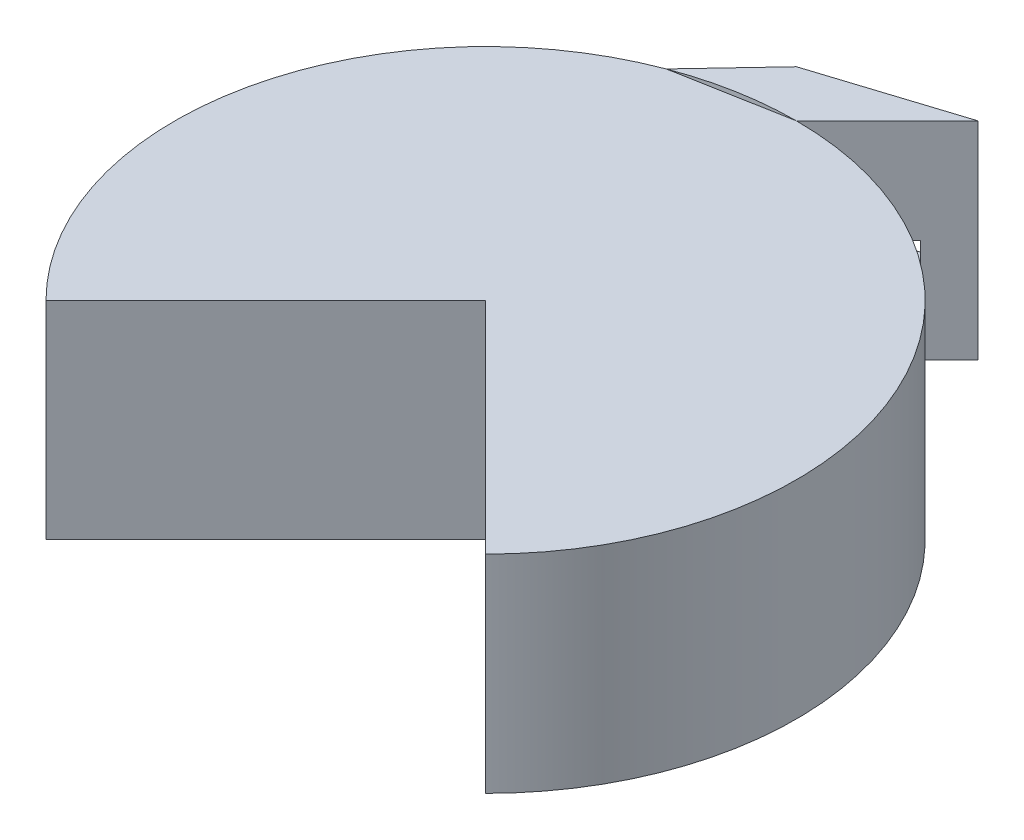
SolidWorks part; units mm, degrees
ref_plane "Front Plane" through (0, 0, 0) normal (0, 0, 1) x (1, 0, 0)
ref_plane "Top Plane" through (0, 0, 0) normal (0, 1, 0) x (1, 0, 0)
ref_plane "Right Plane" through (0, 0, 0) normal (1, 0, 0) x (0, 0, -1)
sketch "Sketch1" plane through (0, 0, 0) normal (0, 1, 0) x (1, 0, 0)
  line L0 (0, 0) -> (-53.033, -53.033)
  line L1 (-53.033, -53.033) -> (0, 0)
  line L2 (53.033, -53.033) -> (0, 0)
  line L3 (0, 0) -> (0, 75)
  line L4 (0, 75) -> (-75, 0)
  line L5 (-75, 0) -> (0, 75)
  line L6 (0, 75) -> (21.9069, 96.9069)
  line L7 (0, 75) -> (-11.3137, 86.3137)
  line L8 (21.9069, 96.9069) -> (-11.3137, 86.3137)
  line L9 (-11.3137, 86.3137) -> (-26.5555, 70.1413)
  line L10 (-26.5555, 70.1413) -> (0, 75)
  circle A0 centre (0, 0) radius 75
  dimension "D1" = 150
  dimension "D2" = 16
  dimension "D3" = 21.9069
extrude "Boss-Extrude2" add sketch "Sketch1" along normal blind 50 contours L2 A0 L3 | L4 A0 L0 L3 | L10 A0 L4 | A0 L7 L9 | L6 L8 L7
sketch "Sketch2" plane through (-26.0271, 0, -81.622) normal (-0.3038, 0, -0.9527) x (-0.9527, 0, 0.3038)
  line L0 (-50.312, 0) -> (-15.4434, 0)
  line L1 (-50.312, 50) -> (-50.312, 25)
  line L2 (-50.312, 50) -> (-50.312, 0) construction
  line L3 (-50.312, 25) -> (-15.4434, 25)
  line L4 (-15.4434, 50) -> (-15.4434, 0) construction
  line L5 (-32.8777, 25) -> (-50.312, 25)
  line L7 (-41.5949, 25) -> (-21.5949, 25)
  line L8 (-41.5949, 25) -> (-41.5949, 19)
  line L9 (-41.5949, 19) -> (-21.5949, 19)
  line L10 (-21.5949, 25) -> (-21.5949, 19)
  dimension "D1" = 6
  dimension "D2" = 20
  dimension "D3" = 8.7172
extrude "Cut-Extrude1" cut sketch "Sketch2" against normal blind 16 contours L10 L3 L5 L8 L9
sketch "Sketch3" plane through (0, 0, 0) normal (0, -1, 0) x (1, 0, 0)
  line L1 (0, 0) -> (-53.033, 53.033) construction
  circle A1 centre (-38.637, 10.3528) radius 18
  arc A2 (-53.033, 53.033) -> (-26.5555, -70.1413) centre (0, 0) ccw construction
  point P3 (-74.7993, 5.4827)
  dimension "D1" = 20
  dimension "D3" = 40
  dimension "D4" = 36
  dimension "D2" = 20
extrude "Cut-Extrude2" cut sketch "Sketch3" against normal blind 30
sketch "Sketch4" plane through (0, 0, 0) normal (0, -1, 0) x (-1, 0, 0)
  line L0 (0, 4.2351) -> (0, 0)
  line L1 (-53.033, -53.033) -> (0, 0) construction
  circle A1 centre (-38.637, -10.3528) radius 18
  dimension "D3" = 36
  dimension "D1" = 40
  dimension "D2" = 20
extrude "Cut-Extrude3" cut sketch "Sketch4" against normal blind 30 contours A1
sketch "Sketch7" plane through (0, 0, 0) normal (0, -1, 0) x (-1, 0, 0)
  circle A1 centre (38.637, 44.282) radius 15
  dimension "D4" = 30
extrude "Cut-Extrude4" cut sketch "Sketch7" against normal blind 30
sketch "Sketch9" plane through (0, 0, 0) normal (0, -1, 0) x (1, 0, 0)
  line L0 (0, -75) -> (-38.637, -44.282)
  line L1 (-38.637, -44.282) -> (-38.637, -64.282)
  line L2 (-38.637, -64.282) -> (-38.637, -44.282)
  arc A0 (-53.033, 53.033) -> (-26.5555, -70.1413) centre (0, 0) ccw construction
  circle A2 centre (38.637, -44.282) radius 15
  dimension "D3" = 30
extrude "Cut-Extrude5" cut sketch "Sketch9" against normal blind 30 contours A2
